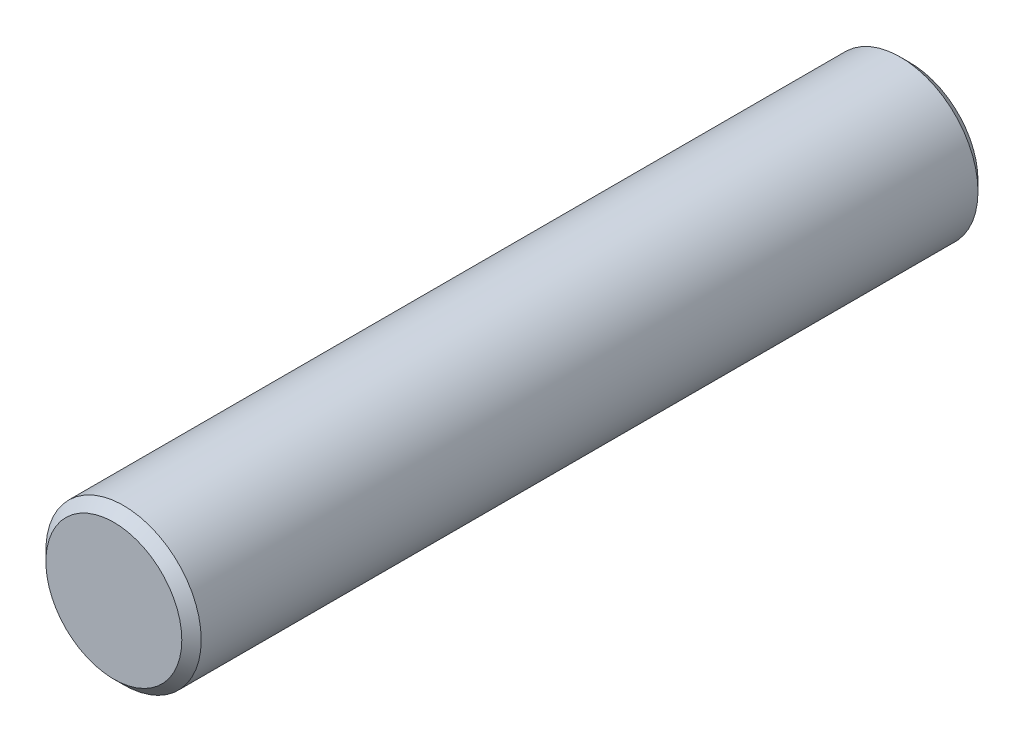
SolidWorks part; units mm, degrees
ref_plane "Front Plane" through (0, 0, 0) normal (0, 0, 1) x (1, 0, 0)
ref_plane "Top Plane" through (0, 0, 0) normal (0, 1, 0) x (1, 0, 0)
ref_plane "Right Plane" through (0, 0, 0) normal (1, 0, 0) x (0, 0, -1)
sketch "Sketch2" plane through (0, 0, 0) normal (0, 0, 1) x (1, 0, 0)
  circle A0 centre (0, 0) radius 8
  dimension "D1" = 16
extrude "Boss-Extrude1" add sketch "Sketch2" along normal mid plane 82
chamfer "Chamfer1" distance 1 angle 45 2 edges at (8, 0, -41) (8, 0, 41)
